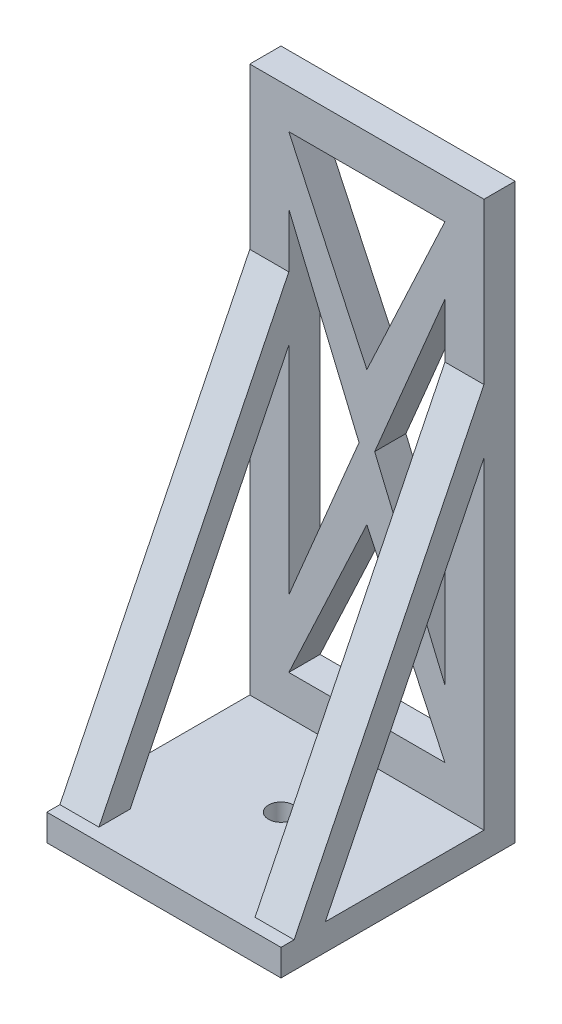
SolidWorks part; units mm, degrees
ref_plane "Front Plane" through (0, 0, 0) normal (0, 0, 1) x (1, 0, 0)
ref_plane "Top Plane" through (0, 0, 0) normal (0, 1, 0) x (1, 0, 0)
ref_plane "Right Plane" through (0, 0, 0) normal (1, 0, 0) x (0, 0, -1)
sketch "Sketch1" plane through (0, 0, 0) normal (0, 1, 0) x (1, 0, 0)
  line L1 (-15, -15) -> (15, -15)
  line L2 (-15, -15) -> (-15, 15)
  line L3 (-15, 15) -> (15, 15)
  line L4 (15, -15) -> (15, 15)
  line L5 (-15, -15) -> (15, 15) construction
  line L6 (-15, 15) -> (15, -15) construction
  circle A0 centre (0, 0) radius 1.6
  point P0 (0, 0)
  dimension "D1" = 3.2
extrude "Boss-Extrude1" add sketch "Sketch1" along normal blind 3.4
sketch "Sketch2" plane through (0, 3.4, 0) normal (0, 1, 0) x (1, 0, 0)
  line L0 (15, -15) -> (15, 15) construction
  line L1 (-15, 15) -> (15, 15)
  line L2 (-15, 15) -> (-15, 11)
  line L3 (-15, 11) -> (15, 11)
  line L4 (15, 15) -> (15, 11)
extrude "Boss-Extrude2" add sketch "Sketch2" along normal blind 70
sketch "Sketch3" plane through (0, 0, -11) normal (0, 0, 1) x (1, 0, 0)
  line L0 (-10, 68.4) -> (10, 68.4) construction
  line L9 (10, 68.4) -> (0, 46.9949) construction
  line L10 (0, 46.9949) -> (-10, 68.4) construction
  line L11 (10, 8.4) -> (0, 29.8051) construction
  line L12 (0, 29.8051) -> (-10, 8.4) construction
  line L13 (-10, 8.4) -> (10, 8.4) construction
  line L14 (0, 46.9949) -> (0, 29.8051) construction
  line L15 (0, 38.4) -> (10, 59.8051) construction
  line L16 (0, 38.4) -> (-10, 16.9949) construction
  line L18 (10, 59.8051) -> (10, 16.9949) construction
  line L19 (10, 16.9949) -> (-10, 59.8051) construction
  line L20 (-10, 59.8051) -> (-10, 16.9949) construction
  line L22 (1, 38.4) -> (10, 16.9949)
  line L23 (10, 16.9949) -> (10, 59.8051)
  line L24 (10, 59.8051) -> (1, 38.4)
  line L26 (-1, 38.4) -> (-10, 59.8051)
  line L27 (-10, 59.8051) -> (-10, 16.9949)
  line L28 (-10, 16.9949) -> (-1, 38.4)
  line L30 (-10, 68.4) -> (0, 46.9949)
  line L31 (0, 46.9949) -> (10, 68.4)
  line L32 (10, 68.4) -> (-10, 68.4)
  line L33 (0, 29.8051) -> (-10, 8.4)
  line L34 (-10, 8.4) -> (10, 8.4)
  line L35 (0, 29.8051) -> (10, 8.4)
  point P4 (0, 38.4)
extrude "Cut-Extrude2" cut sketch "Sketch3" against normal up to next
sketch "Sketch4" plane through (-15, 0, 0) normal (-1, 0, 0) x (0, 0, 1)
  line L0 (-15, 52.8393) -> (-11, 52.8393)
  line L1 (-15, 52.8393) -> (11, 0)
  line L2 (-11, 52.8393) -> (15, 0)
  line L3 (11, 0) -> (15, 0)
  line L4 (-15, 73.4) -> (-15, 0) construction
  line L5 (-11, 73.4) -> (-11, 3.4) construction
extrude "Boss-Extrude3" add sketch "Sketch4" against normal up to surface (5 mm away) up to face at (-10, 38.4, -13)
sketch "Sketch5" plane through (15, 0, 0) normal (1, 0, 0) x (0, 0, -1)
  line L0 (15, 52.8393) -> (11, 52.8393)
  line L1 (15, 52.8393) -> (-11, 0)
  line L2 (11, 52.8393) -> (-15, 0)
  line L3 (-11, 0) -> (-15, 0)
  line L4 (15, 73.4) -> (15, 0) construction
extrude "Boss-Extrude4" add sketch "Sketch5" against normal up to surface (5 mm away) up to face at (10, 38.4, -13)
